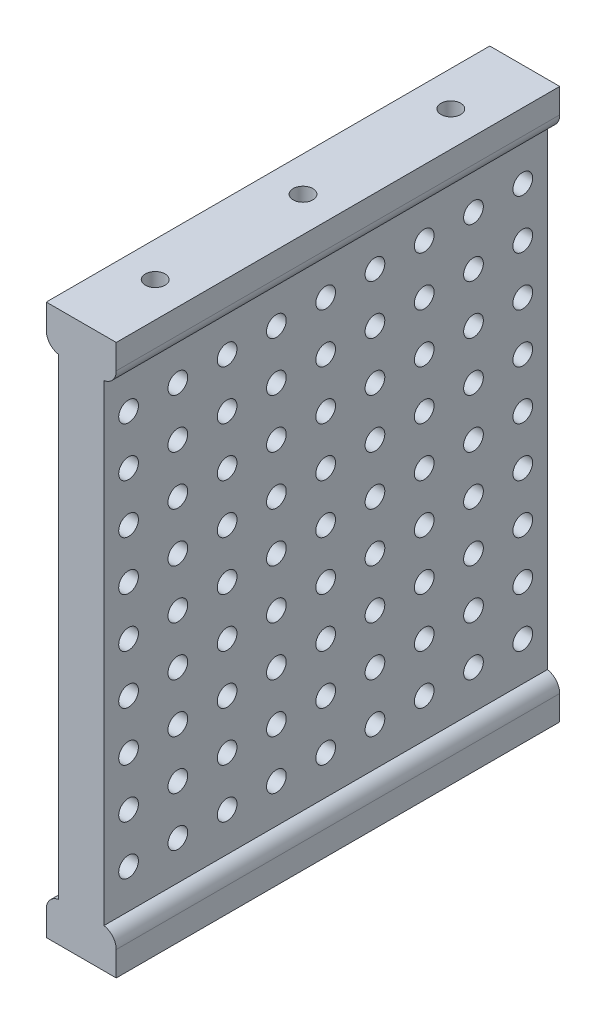
SolidWorks part; units mm, degrees
ref_plane "Plano frontal" through (0, 0, 0) normal (0, 0, 1) x (1, 0, 0)
ref_plane "Plano superior" through (0, 0, 0) normal (0, 1, 0) x (1, 0, 0)
ref_plane "Plano direito" through (0, 0, 0) normal (1, 0, 0) x (0, 0, -1)
sketch "Esboço1" plane through (0, 0, 0) normal (0, 0, 1) x (1, 0, 0)
  line L0 (10.95, -73.1714) -> (10.95, 22.6125)
  line L1 (10.95, -90.2295) -> (10.95, -81.1295)
  line L2 (1.75, -73.1295) -> (1.75, 22.6125)
  line L3 (1.75, 30.5705) -> (10.95, 30.5705)
  line L4 (10.95, -90.2295) -> (10.95, -81.1295)
  line L5 (-0.75, 30.5705) -> (13.45, 30.5705)
  line L6 (-0.75, 30.5705) -> (-0.75, 25.5705)
  line L7 (1.75, -73.1295) -> (1.75, -73.1714)
  line L8 (13.45, 30.5705) -> (13.45, 25.5705)
  line L9 (10.95, -81.1295) -> (10.95, -90.2295)
  line L10 (-0.75, -76.1295) -> (-0.75, -81.1295)
  line L11 (-0.75, -81.1295) -> (13.45, -81.1295)
  line L12 (13.45, -76.1295) -> (13.45, -81.1295)
  arc A0 (-0.75, -76.1295) -> (1.75, -73.1714) centre (2.25, -76.1295) cw
  arc A1 (13.45, -76.1295) -> (10.95, -73.1714) centre (10.45, -76.1295) ccw
  arc A2 (-0.75, 25.5705) -> (1.75, 22.6125) centre (2.25, 25.5705) ccw
  arc A3 (13.45, 25.5705) -> (10.95, 22.6125) centre (10.45, 25.5705) cw
  point P14 (-0.75, -73.1295)
  point P19 (-0.75, 22.5705)
  dimension "D9" = 3
  dimension "D10" = 3
  dimension "D11" = 3
  dimension "D12" = 3
  dimension "D1" = 120.8
  dimension "D2" = 9.2
  dimension "D3" = 14.2
  dimension "D4" = 2.5
  dimension "D5" = 14.2
  dimension "D6" = 2.5
  dimension "D7" = 8
  dimension "D8" = 8
extrude "Ressalto-extrusão2" add sketch "Esboço1" along normal blind 90 contours A3 L8 L5 L3 L6 A2 L2 L7 A0 L10 L11 L12 A1 L1 L4
sketch "Esboço3" plane through (0, 0, 0) normal (0, 1, 0) x (1, 0, 0)
  line L0 (-0.75, 0) -> (13.45, -90) construction
  line L1 (13.45, -90) -> (-0.75, -90) construction
  line L2 (-0.75, -90) -> (13.45, 0) construction
  line L3 (13.45, 0) -> (6.35, 0) construction
  line L4 (-0.75, 0) -> (13.45, 0) construction
  line L5 (6.35, 0) -> (6.35, -90) construction
  line L6 (6.35, -45) -> (6.35, -15) construction
  line L7 (6.35, -45) -> (6.35, -75) construction
  circle A0 centre (6.35, -45) radius 2
  circle A1 centre (6.35, -15) radius 2
  circle A2 centre (6.35, -75) radius 2
  dimension "D1" = 4
  dimension "D2" = 2
  dimension "D3" = 30
  dimension "D5" = 30
  dimension "D4" = 2
extrude "Corte-extrusão1" cut sketch "Esboço3" against normal blind 90 and the other way blind 90
sketch "Esboço4" plane through (0, 0, 0) normal (1, 0, 0) x (0, 0, -1)
  line L5 (-45, -25.2795) -> (-35, -25.2795) construction
  line L6 (-45, -25.2795) -> (-55, -25.2795) construction
  line L7 (-45, -25.2795) -> (-45, -15.2795) construction
  line L8 (-45, -25.2795) -> (-45, -35.2795) construction
  circle A0 centre (-45, -25.2795) radius 2
  circle A1 centre (-35, -25.2795) radius 2
  circle A2 centre (-25, -25.2795) radius 2
  circle A3 centre (-15, -25.2795) radius 2
  circle A4 centre (-5, -25.2795) radius 2
  circle A5 centre (-35, -35.2795) radius 2
  circle A6 centre (-25, -35.2795) radius 2
  circle A7 centre (-15, -35.2795) radius 2
  circle A8 centre (-5, -35.2795) radius 2
  circle A9 centre (-35, -45.2795) radius 2
  circle A10 centre (-25, -45.2795) radius 2
  circle A11 centre (-15, -45.2795) radius 2
  circle A12 centre (-5, -45.2795) radius 2
  circle A13 centre (-35, -55.2795) radius 2
  circle A14 centre (-25, -55.2795) radius 2
  circle A15 centre (-15, -55.2795) radius 2
  circle A16 centre (-5, -55.2795) radius 2
  circle A17 centre (-35, -65.2795) radius 2
  circle A18 centre (-25, -65.2795) radius 2
  circle A19 centre (-15, -65.2795) radius 2
  circle A20 centre (-5, -65.2795) radius 2
  circle A21 centre (-45, -35.2795) radius 2
  circle A22 centre (-45, -45.2795) radius 2
  circle A23 centre (-45, -55.2795) radius 2
  circle A24 centre (-45, -65.2795) radius 2
  circle A25 centre (-55, -25.2795) radius 2
  circle A26 centre (-65, -25.2795) radius 2
  circle A27 centre (-75, -25.2795) radius 2
  circle A28 centre (-85, -25.2795) radius 2
  circle A29 centre (-55, -15.2795) radius 2
  circle A30 centre (-65, -15.2795) radius 2
  circle A31 centre (-75, -15.2795) radius 2
  circle A32 centre (-85, -15.2795) radius 2
  circle A33 centre (-55, -5.2795) radius 2
  circle A34 centre (-65, -5.2795) radius 2
  circle A35 centre (-75, -5.2795) radius 2
  circle A36 centre (-85, -5.2795) radius 2
  circle A37 centre (-55, 4.7205) radius 2
  circle A38 centre (-65, 4.7205) radius 2
  circle A39 centre (-75, 4.7205) radius 2
  circle A40 centre (-85, 4.7205) radius 2
  circle A41 centre (-55, 14.7205) radius 2
  circle A42 centre (-65, 14.7205) radius 2
  circle A43 centre (-75, 14.7205) radius 2
  circle A44 centre (-85, 14.7205) radius 2
  circle A45 centre (-45, -15.2795) radius 2
  circle A46 centre (-45, -5.2795) radius 2
  circle A47 centre (-45, 4.7205) radius 2
  circle A48 centre (-45, 14.7205) radius 2
  circle A49 centre (-45, -15.2795) radius 2
  circle A50 centre (-45, -5.2795) radius 2
  circle A51 centre (-45, 4.7205) radius 2
  circle A52 centre (-45, 14.7205) radius 2
  circle A53 centre (-35, -15.2795) radius 2
  circle A54 centre (-35, -5.2795) radius 2
  circle A55 centre (-35, 4.7205) radius 2
  circle A56 centre (-35, 14.7205) radius 2
  circle A57 centre (-25, -15.2795) radius 2
  circle A58 centre (-25, -5.2795) radius 2
  circle A59 centre (-25, 4.7205) radius 2
  circle A60 centre (-25, 14.7205) radius 2
  circle A61 centre (-15, -15.2795) radius 2
  circle A62 centre (-15, -5.2795) radius 2
  circle A63 centre (-15, 4.7205) radius 2
  circle A64 centre (-15, 14.7205) radius 2
  circle A65 centre (-5, -15.2795) radius 2
  circle A66 centre (-5, -5.2795) radius 2
  circle A67 centre (-5, 4.7205) radius 2
  circle A68 centre (-5, 14.7205) radius 2
  circle A69 centre (-35, -25.2795) radius 2
  circle A70 centre (-25, -25.2795) radius 2
  circle A71 centre (-15, -25.2795) radius 2
  circle A72 centre (-5, -25.2795) radius 2
  circle A73 centre (-45, -35.2795) radius 2
  circle A74 centre (-45, -45.2795) radius 2
  circle A75 centre (-45, -55.2795) radius 2
  circle A76 centre (-45, -65.2795) radius 2
  circle A77 centre (-55, -35.2795) radius 2
  circle A78 centre (-55, -45.2795) radius 2
  circle A79 centre (-55, -55.2795) radius 2
  circle A80 centre (-55, -65.2795) radius 2
  circle A81 centre (-65, -35.2795) radius 2
  circle A82 centre (-65, -45.2795) radius 2
  circle A83 centre (-65, -55.2795) radius 2
  circle A84 centre (-65, -65.2795) radius 2
  circle A85 centre (-75, -35.2795) radius 2
  circle A86 centre (-75, -45.2795) radius 2
  circle A87 centre (-75, -55.2795) radius 2
  circle A88 centre (-75, -65.2795) radius 2
  circle A89 centre (-85, -35.2795) radius 2
  circle A90 centre (-85, -45.2795) radius 2
  circle A91 centre (-85, -55.2795) radius 2
  circle A92 centre (-85, -65.2795) radius 2
  circle A93 centre (-55, -25.2795) radius 2
  circle A94 centre (-65, -25.2795) radius 2
  circle A95 centre (-75, -25.2795) radius 2
  circle A96 centre (-85, -25.2795) radius 2
  dimension "D1" = 4
  dimension "D4" = 10
  dimension "D7" = 10
  dimension "D10" = 10
  dimension "D13" = 10
  dimension "D2" = 5
  dimension "D3" = 5
  dimension "D5" = 5
  dimension "D6" = 5
  dimension "D8" = 5
  dimension "D9" = 5
  dimension "D11" = 5
  dimension "D12" = 5
extrude "Corte-extrusão3" cut sketch "Esboço4" along direction (-1, 0, 0) on the side against the normal blind 24 and the other way blind 39 contours A48 | A47 | A46 | A45 | A0 | A21 | A22 | A23 | A24 | A1 | A2 | A3 | A4 | A25 | A26 | A27 | A28 | A44 | A39 | A34 | A29 | A5 | A10 | A15 | A20 | A92 | A87 | A82 | A77 | A53 | A58 | A63 | A68 | A40 | A36 | A32 | A89 | A90 | A91 | A88 | A84 | A80 | A17 | A18 | A19 | A16 | A12 | A8 | A65 | A66 | A67 | A64 | A60 | A56 | A41 | A42 | A43 | A86 | A85 | A31 | A35 | A38 | A37 | A55 | A59 | A62 | A61 | A7 | A11 | A14 | A13 | A79 | A83 | A78 | A81 | A30 | A33 | A54 | A57 | A6 | A9
